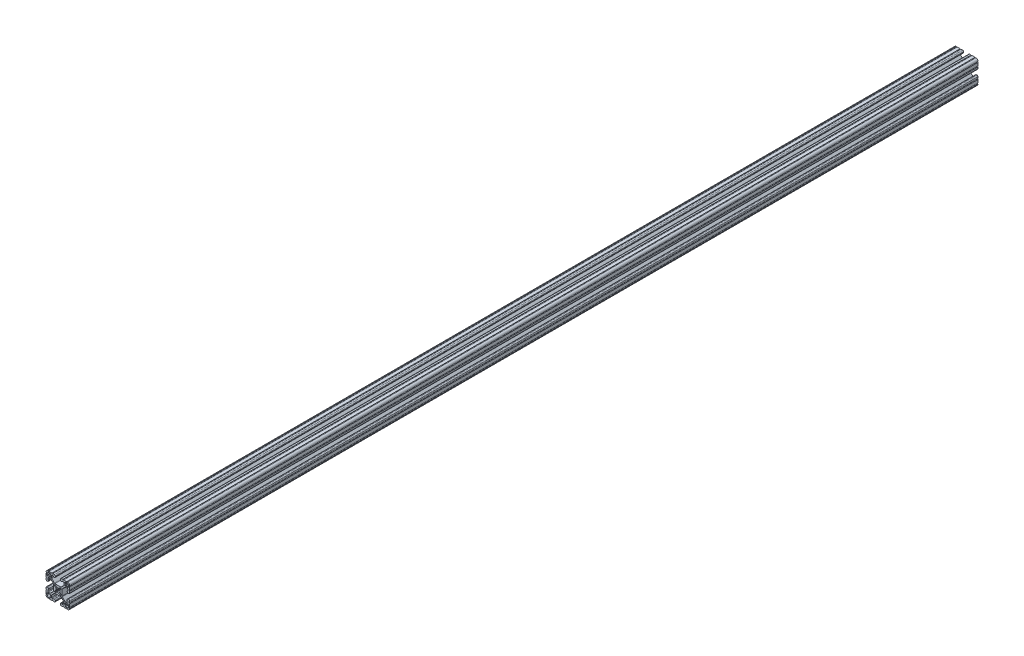
SolidWorks part; units mm, degrees
ref_plane "Front Plane" through (0, 0, 0) normal (0, 0, 1) x (1, 0, 0)
ref_plane "Top Plane" through (0, 0, 0) normal (0, 1, 0) x (1, 0, 0)
ref_plane "Right Plane" through (0, 0, 0) normal (1, 0, 0) x (0, 0, -1)
sketch "Sketch1" plane through (0, 0, 0) normal (0, 0, 1) x (1, 0, 0)
  line L0 (1.5823, 3.1988) -> (3.2921, 4.9085)
  line L1 (3.9207, 5.1689) -> (4.9149, 5.1689)
  line L2 (5.1689, 4.9149) -> (5.1689, 3.9207)
  line L3 (4.9085, 3.2921) -> (3.1988, 1.5823)
  line L4 (3.1988, -1.5823) -> (4.9085, -3.2921)
  line L5 (5.1689, -3.9207) -> (5.1689, -4.9149)
  line L6 (4.9149, -5.1689) -> (3.9207, -5.1689)
  line L7 (3.2921, -4.9085) -> (1.5823, -3.1988)
  line L8 (-1.5823, -3.1988) -> (-3.2921, -4.9085)
  line L9 (-3.9207, -5.1689) -> (-4.9149, -5.1689)
  line L10 (-5.1689, -4.9149) -> (-5.1689, -3.9207)
  line L11 (-4.9085, -3.2921) -> (-3.1988, -1.5823)
  line L12 (-3.1988, 1.5823) -> (-4.9085, 3.2921)
  line L13 (-5.1689, 3.9207) -> (-5.1689, 4.9149)
  line L14 (-4.9149, 5.1689) -> (-3.9207, 5.1689)
  line L15 (-3.2921, 4.9085) -> (-1.5823, 3.1988)
  line L16 (-11.8669, 14.0194) -> (-11.8669, 12.2479)
  line L17 (-12.2479, 11.8669) -> (-14.0195, 11.8669)
  line L18 (-14.0213, 11.8676) -> (-14.5575, 12.4039)
  line L19 (-14.5611, 12.4039) -> (-15.0973, 11.8676)
  line L20 (-15.0991, 11.8669) -> (-16.8707, 11.8669)
  line L21 (-17.2517, 12.2479) -> (-17.2517, 14.4577)
  line L22 (-14.4577, 17.2517) -> (-12.2479, 17.2517)
  line L23 (-11.8669, 16.8707) -> (-11.8669, 15.0991)
  line L24 (-11.8676, 15.0973) -> (-12.4039, 14.5611)
  line L25 (-12.4039, 14.5575) -> (-11.8676, 14.0212)
  line L26 (-14.0194, -11.8669) -> (-12.2479, -11.8669)
  line L27 (-11.8669, -12.2479) -> (-11.8669, -14.0195)
  line L28 (-11.8676, -14.0213) -> (-12.4039, -14.5575)
  line L29 (-12.4039, -14.5611) -> (-11.8676, -15.0973)
  line L30 (-11.8669, -15.0991) -> (-11.8669, -16.8707)
  line L31 (-12.2479, -17.2517) -> (-14.4577, -17.2517)
  line L32 (-17.2517, -14.4577) -> (-17.2517, -12.2479)
  line L33 (-16.8707, -11.8669) -> (-15.0991, -11.8669)
  line L34 (-15.0973, -11.8676) -> (-14.5611, -12.4039)
  line L35 (-14.5575, -12.4039) -> (-14.0212, -11.8676)
  line L36 (11.8669, -14.0194) -> (11.8669, -12.2479)
  line L37 (12.2479, -11.8669) -> (14.0195, -11.8669)
  line L38 (14.0213, -11.8676) -> (14.5575, -12.4039)
  line L39 (14.5611, -12.4039) -> (15.0973, -11.8676)
  line L40 (15.0991, -11.8669) -> (16.8707, -11.8669)
  line L41 (17.2517, -12.2479) -> (17.2517, -14.4577)
  line L42 (14.4577, -17.2517) -> (12.2479, -17.2517)
  line L43 (11.8669, -16.8707) -> (11.8669, -15.0991)
  line L44 (11.8676, -15.0973) -> (12.4039, -14.5611)
  line L45 (12.4039, -14.5575) -> (11.8676, -14.0212)
  line L46 (14.0194, 11.8669) -> (12.2479, 11.8669)
  line L47 (11.8669, 12.2479) -> (11.8669, 14.0195)
  line L48 (11.8676, 14.0213) -> (12.4039, 14.5575)
  line L49 (12.4039, 14.5611) -> (11.8676, 15.0973)
  line L50 (11.8669, 15.0991) -> (11.8669, 16.8707)
  line L51 (12.2479, 17.2517) -> (14.4577, 17.2517)
  line L52 (17.2517, 14.4577) -> (17.2517, 12.2479)
  line L53 (16.8707, 11.8669) -> (15.0991, 11.8669)
  line L54 (15.0973, 11.8676) -> (14.5611, 12.4039)
  line L55 (14.5575, 12.4039) -> (14.0212, 11.8676)
  line L56 (6.3498, -14.9848) -> (5.6531, -14.9848)
  line L57 (4.0778, -16.5601) -> (4.0778, -17.4747)
  line L58 (5.6531, -19.05) -> (7.9756, -19.05)
  line L59 (9.4996, -19.05) -> (14.2981, -19.05)
  line L60 (19.05, -14.3256) -> (19.05, -9.4996)
  line L61 (19.05, -7.9756) -> (19.05, -5.6531)
  line L62 (17.4747, -4.0778) -> (16.5601, -4.0778)
  line L63 (14.9848, -5.6531) -> (14.9848, -6.3498)
  line L64 (15.3661, -6.731) -> (15.6969, -6.731)
  line L65 (16.0782, -7.1122) -> (16.0782, -9.3968)
  line L66 (15.1881, -10.287) -> (12.3526, -10.2871)
  line L67 (11.4535, -9.9142) -> (7.1147, -5.5659)
  line L68 (6.7437, -4.6689) -> (6.7437, 4.6414)
  line L69 (7.1147, 5.5384) -> (11.481, 9.9142)
  line L70 (12.38, 10.2871) -> (15.1881, 10.287)
  line L71 (16.0782, 9.3968) -> (16.0782, 7.1122)
  line L72 (15.6969, 6.731) -> (15.3661, 6.731)
  line L73 (14.9848, 6.3498) -> (14.9848, 5.6531)
  line L74 (16.5601, 4.0778) -> (17.4747, 4.0778)
  line L75 (19.05, 5.6531) -> (19.05, 7.9756)
  line L76 (19.05, 9.4996) -> (19.05, 14.2981)
  line L77 (14.3256, 19.05) -> (9.4996, 19.05)
  line L78 (7.9756, 19.05) -> (5.6531, 19.05)
  line L79 (4.0778, 17.4747) -> (4.0778, 16.5601)
  line L80 (5.6531, 14.9848) -> (6.3498, 14.9848)
  line L81 (6.731, 15.3661) -> (6.731, 15.6969)
  line L82 (7.1122, 16.0782) -> (9.3968, 16.0782)
  line L83 (10.287, 15.1881) -> (10.2871, 12.3526)
  line L84 (9.9142, 11.4535) -> (5.5659, 7.1147)
  line L85 (4.6689, 6.7437) -> (-4.6414, 6.7437)
  line L86 (-5.5384, 7.1147) -> (-9.9142, 11.481)
  line L87 (-10.2871, 12.38) -> (-10.287, 15.1881)
  line L88 (-9.3968, 16.0782) -> (-7.1122, 16.0782)
  line L89 (-6.731, 15.6969) -> (-6.731, 15.3661)
  line L90 (-6.3498, 14.9848) -> (-5.6531, 14.9848)
  line L91 (-4.0778, 16.5601) -> (-4.0778, 17.4747)
  line L92 (-5.6531, 19.05) -> (-7.9756, 19.05)
  line L93 (-9.4996, 19.05) -> (-14.2981, 19.05)
  line L94 (-19.05, 14.3256) -> (-19.05, 9.4996)
  line L95 (-19.05, 7.9756) -> (-19.05, 5.6531)
  line L96 (-17.4747, 4.0778) -> (-16.5601, 4.0778)
  line L97 (-14.9848, 5.6531) -> (-14.9848, 6.3498)
  line L98 (-15.3661, 6.731) -> (-15.6969, 6.731)
  line L99 (-16.0782, 7.1122) -> (-16.0782, 9.3968)
  line L100 (-15.1881, 10.287) -> (-12.3526, 10.2871)
  line L101 (-11.4535, 9.9142) -> (-7.1147, 5.5659)
  line L102 (-6.7437, 4.6689) -> (-6.7437, -4.6414)
  line L103 (-7.1147, -5.5384) -> (-11.481, -9.9142)
  line L104 (-12.38, -10.2871) -> (-15.1881, -10.287)
  line L105 (-16.0782, -9.3968) -> (-16.0782, -7.1122)
  line L106 (-15.6969, -6.731) -> (-15.3661, -6.731)
  line L107 (-14.9848, -6.3498) -> (-14.9848, -5.6531)
  line L108 (-16.5601, -4.0778) -> (-17.4747, -4.0778)
  line L109 (-19.05, -5.6531) -> (-19.05, -7.9756)
  line L110 (-19.05, -9.4996) -> (-19.05, -14.2981)
  line L111 (-14.3256, -19.05) -> (-9.4996, -19.05)
  line L112 (-7.9756, -19.05) -> (-5.6531, -19.05)
  line L113 (-4.0778, -17.4747) -> (-4.0778, -16.5601)
  line L114 (-5.6531, -14.9848) -> (-6.3498, -14.9848)
  line L115 (-6.731, -15.3661) -> (-6.731, -15.6969)
  line L116 (-7.1122, -16.0782) -> (-9.3968, -16.0782)
  line L117 (-10.287, -15.1881) -> (-10.2871, -12.3526)
  line L118 (-9.9142, -11.4535) -> (-5.5659, -7.1147)
  line L119 (-4.6689, -6.7437) -> (4.6414, -6.7437)
  line L120 (5.5384, -7.1147) -> (9.9142, -11.481)
  line L121 (10.2871, -12.38) -> (10.287, -15.1881)
  line L122 (9.3968, -16.0782) -> (7.1122, -16.0782)
  line L123 (6.731, -15.6969) -> (6.731, -15.3661)
  arc A0 (1.178, 3.1119) -> (1.5823, 3.1988) centre (1.3129, 3.4682) ccw
  arc A1 (3.9207, 5.1689) -> (3.2921, 4.9085) centre (3.9207, 4.2799) ccw
  arc A2 (5.1689, 4.9149) -> (4.9149, 5.1689) centre (4.9149, 4.9149) ccw
  arc A3 (4.9085, 3.2921) -> (5.1689, 3.9207) centre (4.2799, 3.9207) ccw
  arc A4 (3.1988, 1.5823) -> (3.1119, 1.178) centre (3.4682, 1.3129) ccw
  arc A5 (3.1119, -1.178) -> (3.1119, 1.178) centre (0, 0) ccw
  arc A6 (3.1119, -1.178) -> (3.1988, -1.5823) centre (3.4682, -1.3129) ccw
  arc A7 (5.1689, -3.9207) -> (4.9085, -3.2921) centre (4.2799, -3.9207) ccw
  arc A8 (4.9149, -5.1689) -> (5.1689, -4.9149) centre (4.9149, -4.9149) ccw
  arc A9 (3.2921, -4.9085) -> (3.9207, -5.1689) centre (3.9207, -4.2799) ccw
  arc A10 (1.5823, -3.1988) -> (1.178, -3.1119) centre (1.3129, -3.4682) ccw
  arc A11 (-1.178, -3.1119) -> (1.178, -3.1119) centre (0, 0) ccw
  arc A12 (-1.178, -3.1119) -> (-1.5823, -3.1988) centre (-1.3129, -3.4682) ccw
  arc A13 (-3.9207, -5.1689) -> (-3.2921, -4.9085) centre (-3.9207, -4.2799) ccw
  arc A14 (-5.1689, -4.9149) -> (-4.9149, -5.1689) centre (-4.9149, -4.9149) ccw
  arc A15 (-4.9085, -3.2921) -> (-5.1689, -3.9207) centre (-4.2799, -3.9207) ccw
  arc A16 (-3.1988, -1.5823) -> (-3.1119, -1.178) centre (-3.4682, -1.3129) ccw
  arc A17 (-3.1119, 1.178) -> (-3.1119, -1.178) centre (0, 0) ccw
  arc A18 (-3.1119, 1.178) -> (-3.1988, 1.5823) centre (-3.4682, 1.3129) ccw
  arc A19 (-5.1689, 3.9207) -> (-4.9085, 3.2921) centre (-4.2799, 3.9207) ccw
  arc A20 (-4.9149, 5.1689) -> (-5.1689, 4.9149) centre (-4.9149, 4.9149) ccw
  arc A21 (-3.2921, 4.9085) -> (-3.9207, 5.1689) centre (-3.9207, 4.2799) ccw
  arc A22 (-1.5823, 3.1988) -> (-1.178, 3.1119) centre (-1.3129, 3.4682) ccw
  arc A23 (1.178, 3.1119) -> (-1.178, 3.1119) centre (0, 0) ccw
  arc A24 (-11.8669, 14.0194) -> (-11.8676, 14.0212) centre (-11.8694, 14.0194) ccw
  arc A25 (-12.2479, 11.8669) -> (-11.8669, 12.2479) centre (-12.2479, 12.2479) ccw
  arc A26 (-14.0213, 11.8676) -> (-14.0195, 11.8669) centre (-14.0195, 11.8694) ccw
  arc A27 (-14.5575, 12.4039) -> (-14.5611, 12.4039) centre (-14.5593, 12.4021) ccw
  arc A28 (-15.0991, 11.8669) -> (-15.0973, 11.8676) centre (-15.0991, 11.8694) ccw
  arc A29 (-17.2517, 12.2479) -> (-16.8707, 11.8669) centre (-16.8707, 12.2479) ccw
  arc A30 (-14.4577, 17.2517) -> (-17.2517, 14.4577) centre (-14.4577, 14.4577) ccw
  arc A31 (-11.8669, 16.8707) -> (-12.2479, 17.2517) centre (-12.2479, 16.8707) ccw
  arc A32 (-11.8676, 15.0973) -> (-11.8669, 15.0991) centre (-11.8694, 15.0991) ccw
  arc A33 (-12.4039, 14.5611) -> (-12.4039, 14.5575) centre (-12.4021, 14.5593) ccw
  arc A34 (-14.0194, -11.8669) -> (-14.0212, -11.8676) centre (-14.0194, -11.8694) ccw
  arc A35 (-11.8669, -12.2479) -> (-12.2479, -11.8669) centre (-12.2479, -12.2479) ccw
  arc A36 (-11.8676, -14.0213) -> (-11.8669, -14.0195) centre (-11.8694, -14.0195) ccw
  arc A37 (-12.4039, -14.5575) -> (-12.4039, -14.5611) centre (-12.4021, -14.5593) ccw
  arc A38 (-11.8669, -15.0991) -> (-11.8676, -15.0973) centre (-11.8694, -15.0991) ccw
  arc A39 (-12.2479, -17.2517) -> (-11.8669, -16.8707) centre (-12.2479, -16.8707) ccw
  arc A40 (-17.2517, -14.4577) -> (-14.4577, -17.2517) centre (-14.4577, -14.4577) ccw
  arc A41 (-16.8707, -11.8669) -> (-17.2517, -12.2479) centre (-16.8707, -12.2479) ccw
  arc A42 (-15.0973, -11.8676) -> (-15.0991, -11.8669) centre (-15.0991, -11.8694) ccw
  arc A43 (-14.5611, -12.4039) -> (-14.5575, -12.4039) centre (-14.5593, -12.4021) ccw
  arc A44 (11.8669, -14.0194) -> (11.8676, -14.0212) centre (11.8694, -14.0194) ccw
  arc A45 (12.2479, -11.8669) -> (11.8669, -12.2479) centre (12.2479, -12.2479) ccw
  arc A46 (14.0213, -11.8676) -> (14.0195, -11.8669) centre (14.0195, -11.8694) ccw
  arc A47 (14.5575, -12.4039) -> (14.5611, -12.4039) centre (14.5593, -12.4021) ccw
  arc A48 (15.0991, -11.8669) -> (15.0973, -11.8676) centre (15.0991, -11.8694) ccw
  arc A49 (17.2517, -12.2479) -> (16.8707, -11.8669) centre (16.8707, -12.2479) ccw
  arc A50 (14.4577, -17.2517) -> (17.2517, -14.4577) centre (14.4577, -14.4577) ccw
  arc A51 (11.8669, -16.8707) -> (12.2479, -17.2517) centre (12.2479, -16.8707) ccw
  arc A52 (11.8676, -15.0973) -> (11.8669, -15.0991) centre (11.8694, -15.0991) ccw
  arc A53 (12.4039, -14.5611) -> (12.4039, -14.5575) centre (12.4021, -14.5593) ccw
  arc A54 (14.0194, 11.8669) -> (14.0212, 11.8676) centre (14.0194, 11.8694) ccw
  arc A55 (11.8669, 12.2479) -> (12.2479, 11.8669) centre (12.2479, 12.2479) ccw
  arc A56 (11.8676, 14.0213) -> (11.8669, 14.0195) centre (11.8694, 14.0195) ccw
  arc A57 (12.4039, 14.5575) -> (12.4039, 14.5611) centre (12.4021, 14.5593) ccw
  arc A58 (11.8669, 15.0991) -> (11.8676, 15.0973) centre (11.8694, 15.0991) ccw
  arc A59 (12.2479, 17.2517) -> (11.8669, 16.8707) centre (12.2479, 16.8707) ccw
  arc A60 (17.2517, 14.4577) -> (14.4577, 17.2517) centre (14.4577, 14.4577) ccw
  arc A61 (16.8707, 11.8669) -> (17.2517, 12.2479) centre (16.8707, 12.2479) ccw
  arc A62 (15.0973, 11.8676) -> (15.0991, 11.8669) centre (15.0991, 11.8694) ccw
  arc A63 (14.5611, 12.4039) -> (14.5575, 12.4039) centre (14.5593, 12.4021) ccw
  arc A64 (6.731, -15.3661) -> (6.3498, -14.9848) centre (6.35, -15.3658) ccw
  arc A65 (5.6531, -14.9848) -> (4.0778, -16.5601) centre (5.6526, -16.5596) ccw
  arc A66 (4.0778, -17.4747) -> (5.6531, -19.05) centre (5.6526, -17.4752) ccw
  arc A67 (9.4996, -19.05) -> (7.9756, -19.05) centre (8.7376, -19.05) ccw
  arc A68 (15.8221, -19.0496) -> (14.2981, -19.05) centre (15.0601, -19.05) ccw
  arc A69 (15.8221, -19.0496) -> (19.0499, -15.8496) centre (15.875, -15.875) ccw
  arc A70 (19.05, -14.3256) -> (19.0499, -15.8496) centre (19.05, -15.0876) ccw
  arc A71 (19.05, -7.9756) -> (19.05, -9.4996) centre (19.05, -8.7376) ccw
  arc A72 (19.05, -5.6531) -> (17.4747, -4.0778) centre (17.4752, -5.6526) ccw
  arc A73 (16.5601, -4.0778) -> (14.9848, -5.6531) centre (16.5596, -5.6526) ccw
  arc A74 (14.9848, -6.3498) -> (15.3661, -6.731) centre (15.3658, -6.35) ccw
  arc A75 (16.0782, -7.1122) -> (15.6969, -6.731) centre (15.6972, -7.112) ccw
  arc A76 (15.1881, -10.287) -> (16.0782, -9.3968) centre (15.1892, -9.398) ccw
  arc A77 (11.4535, -9.9142) -> (12.3526, -10.2871) centre (12.3525, -9.0171) ccw
  arc A78 (6.7437, -4.6689) -> (7.1147, -5.5659) centre (8.0137, -4.6689) ccw
  arc A79 (7.1147, 5.5384) -> (6.7437, 4.6414) centre (8.0137, 4.6414) ccw
  arc A80 (12.38, 10.2871) -> (11.481, 9.9142) centre (12.38, 9.0171) ccw
  arc A81 (16.0782, 9.3968) -> (15.1881, 10.287) centre (15.1892, 9.398) ccw
  arc A82 (15.6969, 6.731) -> (16.0782, 7.1122) centre (15.6972, 7.112) ccw
  arc A83 (15.3661, 6.731) -> (14.9848, 6.3498) centre (15.3658, 6.35) ccw
  arc A84 (14.9848, 5.6531) -> (16.5601, 4.0778) centre (16.5596, 5.6526) ccw
  arc A85 (17.4747, 4.0778) -> (19.05, 5.6531) centre (17.4752, 5.6526) ccw
  arc A86 (19.05, 9.4996) -> (19.05, 7.9756) centre (19.05, 8.7376) ccw
  arc A87 (19.0496, 15.8221) -> (19.05, 14.2981) centre (19.05, 15.0601) ccw
  arc A88 (19.0496, 15.8221) -> (15.8496, 19.0499) centre (15.875, 15.875) ccw
  arc A89 (14.3256, 19.05) -> (15.8496, 19.0499) centre (15.0876, 19.05) ccw
  arc A90 (7.9756, 19.05) -> (9.4996, 19.05) centre (8.7376, 19.05) ccw
  arc A91 (5.6531, 19.05) -> (4.0778, 17.4747) centre (5.6526, 17.4752) ccw
  arc A92 (4.0778, 16.5601) -> (5.6531, 14.9848) centre (5.6526, 16.5596) ccw
  arc A93 (6.3498, 14.9848) -> (6.731, 15.3661) centre (6.35, 15.3658) ccw
  arc A94 (7.1122, 16.0782) -> (6.731, 15.6969) centre (7.112, 15.6972) ccw
  arc A95 (10.287, 15.1881) -> (9.3968, 16.0782) centre (9.398, 15.1892) ccw
  arc A96 (9.9142, 11.4535) -> (10.2871, 12.3526) centre (9.0171, 12.3525) ccw
  arc A97 (4.6689, 6.7437) -> (5.5659, 7.1147) centre (4.6689, 8.0137) ccw
  arc A98 (-5.5384, 7.1147) -> (-4.6414, 6.7437) centre (-4.6414, 8.0137) ccw
  arc A99 (-10.2871, 12.38) -> (-9.9142, 11.481) centre (-9.0171, 12.38) ccw
  arc A100 (-9.3968, 16.0782) -> (-10.287, 15.1881) centre (-9.398, 15.1892) ccw
  arc A101 (-6.731, 15.6969) -> (-7.1122, 16.0782) centre (-7.112, 15.6972) ccw
  arc A102 (-6.731, 15.3661) -> (-6.3498, 14.9848) centre (-6.35, 15.3658) ccw
  arc A103 (-5.6531, 14.9848) -> (-4.0778, 16.5601) centre (-5.6526, 16.5596) ccw
  arc A104 (-4.0778, 17.4747) -> (-5.6531, 19.05) centre (-5.6526, 17.4752) ccw
  arc A105 (-9.4996, 19.05) -> (-7.9756, 19.05) centre (-8.7376, 19.05) ccw
  arc A106 (-15.8221, 19.0496) -> (-14.2981, 19.05) centre (-15.0601, 19.05) ccw
  arc A107 (-15.8221, 19.0496) -> (-19.0499, 15.8496) centre (-15.875, 15.875) ccw
  arc A108 (-19.05, 14.3256) -> (-19.0499, 15.8496) centre (-19.05, 15.0876) ccw
  arc A109 (-19.05, 7.9756) -> (-19.05, 9.4996) centre (-19.05, 8.7376) ccw
  arc A110 (-19.05, 5.6531) -> (-17.4747, 4.0778) centre (-17.4752, 5.6526) ccw
  arc A111 (-16.5601, 4.0778) -> (-14.9848, 5.6531) centre (-16.5596, 5.6526) ccw
  arc A112 (-14.9848, 6.3498) -> (-15.3661, 6.731) centre (-15.3658, 6.35) ccw
  arc A113 (-16.0782, 7.1122) -> (-15.6969, 6.731) centre (-15.6972, 7.112) ccw
  arc A114 (-15.1881, 10.287) -> (-16.0782, 9.3968) centre (-15.1892, 9.398) ccw
  arc A115 (-11.4535, 9.9142) -> (-12.3526, 10.2871) centre (-12.3525, 9.0171) ccw
  arc A116 (-6.7437, 4.6689) -> (-7.1147, 5.5659) centre (-8.0137, 4.6689) ccw
  arc A117 (-7.1147, -5.5384) -> (-6.7437, -4.6414) centre (-8.0137, -4.6414) ccw
  arc A118 (-12.38, -10.2871) -> (-11.481, -9.9142) centre (-12.38, -9.0171) ccw
  arc A119 (-16.0782, -9.3968) -> (-15.1881, -10.287) centre (-15.1892, -9.398) ccw
  arc A120 (-15.6969, -6.731) -> (-16.0782, -7.1122) centre (-15.6972, -7.112) ccw
  arc A121 (-15.3661, -6.731) -> (-14.9848, -6.3498) centre (-15.3658, -6.35) ccw
  arc A122 (-14.9848, -5.6531) -> (-16.5601, -4.0778) centre (-16.5596, -5.6526) ccw
  arc A123 (-17.4747, -4.0778) -> (-19.05, -5.6531) centre (-17.4752, -5.6526) ccw
  arc A124 (-19.05, -9.4996) -> (-19.05, -7.9756) centre (-19.05, -8.7376) ccw
  arc A125 (-19.0496, -15.8221) -> (-19.05, -14.2981) centre (-19.05, -15.0601) ccw
  arc A126 (-19.0496, -15.8221) -> (-15.8496, -19.0499) centre (-15.875, -15.875) ccw
  arc A127 (-14.3256, -19.05) -> (-15.8496, -19.0499) centre (-15.0876, -19.05) ccw
  arc A128 (-7.9756, -19.05) -> (-9.4996, -19.05) centre (-8.7376, -19.05) ccw
  arc A129 (-5.6531, -19.05) -> (-4.0778, -17.4747) centre (-5.6526, -17.4752) ccw
  arc A130 (-4.0778, -16.5601) -> (-5.6531, -14.9848) centre (-5.6526, -16.5596) ccw
  arc A131 (-6.3498, -14.9848) -> (-6.731, -15.3661) centre (-6.35, -15.3658) ccw
  arc A132 (-7.1122, -16.0782) -> (-6.731, -15.6969) centre (-7.112, -15.6972) ccw
  arc A133 (-10.287, -15.1881) -> (-9.3968, -16.0782) centre (-9.398, -15.1892) ccw
  arc A134 (-9.9142, -11.4535) -> (-10.2871, -12.3526) centre (-9.0171, -12.3525) ccw
  arc A135 (-4.6689, -6.7437) -> (-5.5659, -7.1147) centre (-4.6689, -8.0137) ccw
  arc A136 (5.5384, -7.1147) -> (4.6414, -6.7437) centre (4.6414, -8.0137) ccw
  arc A137 (10.2871, -12.38) -> (9.9142, -11.481) centre (9.0171, -12.38) ccw
  arc A138 (9.3968, -16.0782) -> (10.287, -15.1881) centre (9.398, -15.1892) ccw
  arc A139 (6.731, -15.6969) -> (7.1122, -16.0782) centre (7.112, -15.6972) ccw
extrude "Extrude1" add sketch "Sketch1" against normal blind 1460.5
